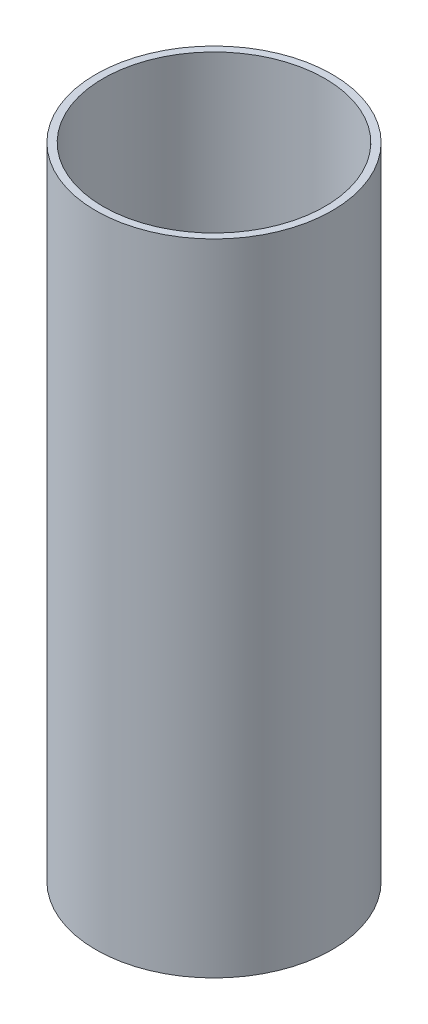
SolidWorks part; units mm, degrees
ref_plane "Front Plane" through (0, 0, 0) normal (0, 0, 1) x (1, 0, 0)
ref_plane "Top Plane" through (0, 0, 0) normal (0, 1, 0) x (1, 0, 0)
ref_plane "Right Plane" through (0, 0, 0) normal (1, 0, 0) x (0, 0, -1)
sketch "Sketch1" plane through (0, 0, 0) normal (0, 0, 1) x (1, 0, 0)
  line L1 (48.4188, 0) -> (51.5938, 0)
  line L2 (48.4188, 0) -> (48.4188, 279.4)
  line L3 (48.4188, 279.4) -> (51.5938, 279.4)
  line L4 (51.5938, 0) -> (51.5938, 279.4)
  dimension "D1" = 51.5938
  dimension "D2" = 3.175
  dimension "D3" = 279.4
  dimension "D4" = 0
ref_axis "Axis1" through (0, -13.97, 0) along (0, 1, 0)
revolve "Revolve1" add sketch "Sketch1" angle 360 about axis through (0, -13.97, 0) along (0, 1, 0)
